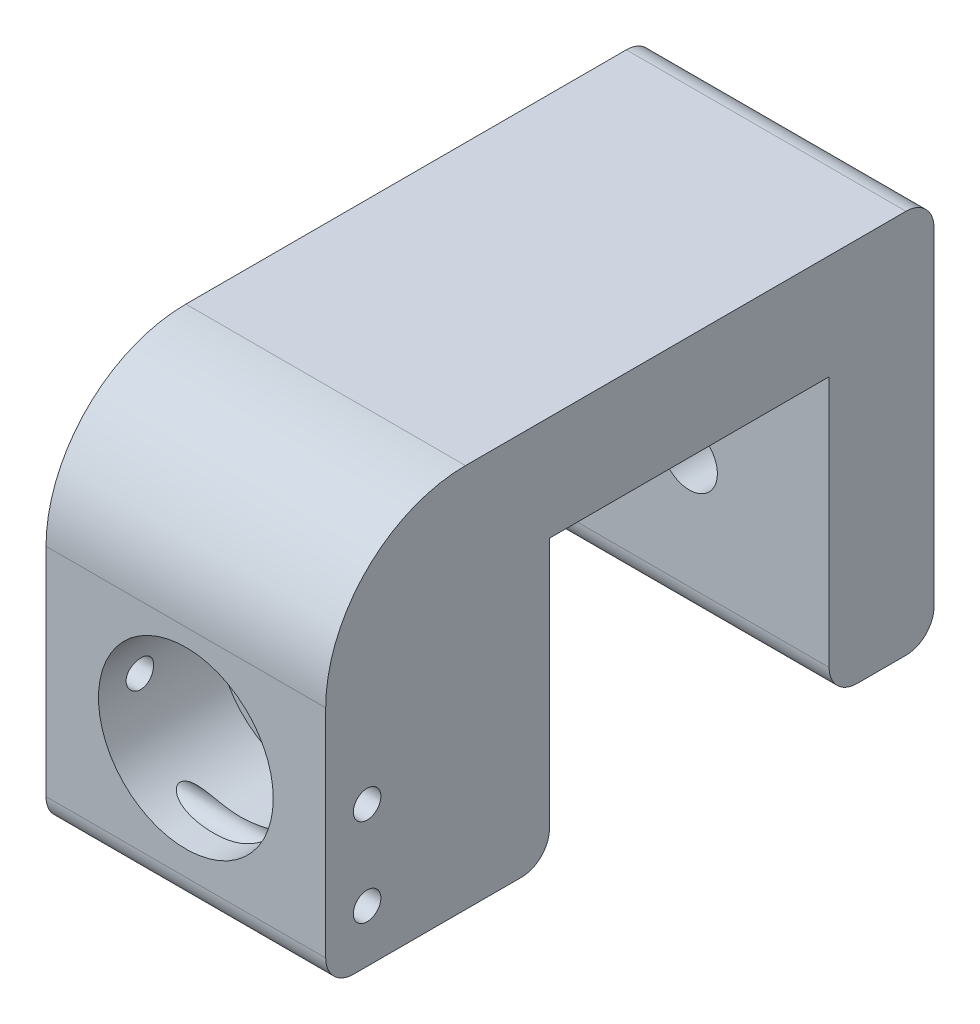
SolidWorks part; units mm, degrees
material "PET"
ref_plane "Front" through (0, 0, 0) normal (0, 0, 1) x (1, 0, 0)
ref_plane "Top" through (0, 0, 0) normal (0, 1, 0) x (1, 0, 0)
ref_plane "Right" through (0, 0, 0) normal (1, 0, 0) x (0, 0, -1)
sketch "Sketch1" plane through (0, 0, 0) normal (1, 0, 0) x (0, 0, -1)
  line L0 (0, 0) -> (0, -25.4)
  line L1 (0, -25.4) -> (-20.32, -25.4)
  line L2 (-20.32, -25.4) -> (-20.32, -3.175)
  line L3 (-7.62, 9.525) -> (34.925, 9.525)
  line L4 (34.925, 9.525) -> (34.925, -25.4)
  line L5 (34.925, -25.4) -> (25.4, -25.4)
  line L6 (25.4, -25.4) -> (25.4, 0)
  line L7 (25.4, 0) -> (0, 0)
  arc A0 (-20.32, -3.175) -> (-7.62, 9.525) centre (-7.62, -3.175) cw
  point P4 (0, 0)
  dimension "D6" = 12.7
  dimension "D1" = 25.4
  dimension "D2" = 25.4
  dimension "D3" = 9.525
  dimension "D4" = 9.525
  dimension "D5" = 20.32
extrude "Boss-Extrude1" add sketch "Sketch1" along normal blind 25.4
sketch "Sketch4" plane through (0, 0, 0) normal (0, 0, -1) x (-1, 0, 0)
  line L0 (-25.4, 0) -> (0, -25.4) construction
  point P0 (-12.7, -12.7)
hole_wizard "1/4 (0.2500) Dowel Hole1" positions "Sketch4" profile "Sketch3" hole size "1/4" standard "ANSI Inch"
sketch "Sketch3" plane through (12.7, -12.7, 0) normal (1, 0, 0) x (0, 1, 0)
  line L0 (0, 0) -> (0, 20.32)
  line L1 (0, 20.32) -> (3.175, 20.32)
  line L2 (3.175, 20.32) -> (3.175, 0)
  line L5 (3.175, 0) -> (0, 0)
  line L11 (0, -6.35) -> (0, 107.95) construction
  dimension "Thru Hole Dia." = 6.35
  dimension "Thru Hole Depth" = 20.32
sketch "Sketch7" plane through (0, 0, -34.925) normal (0, 0, -1) x (-1, 0, 0)
  circle A0 centre (-12.7, -12.7) radius 3.175 construction
  point P0 (-12.7, -12.7)
hole_wizard "#10 Clearance Hole1" positions "Sketch7" profile "Sketch6" hole size "#10" standard "ANSI Inch" end condition through all
sketch "Sketch6" plane through (12.7, -12.7, -34.925) normal (1, 0, 0) x (0, 1, 0)
  line L0 (0, 0) -> (0, 55.245)
  line L1 (0, 55.245) -> (2.5527, 55.245)
  line L2 (2.5527, 55.245) -> (2.5527, 0)
  line L5 (2.5527, 0) -> (0, 0)
  line L11 (0, -6.35) -> (0, 107.95) construction
  dimension "Thru Hole Dia." = 5.1054
  dimension "Thru Hole Depth" = 55.245
sketch "Sketch8" plane through (0, 0, 20.32) normal (0, 0, 1) x (1, 0, 0)
  circle A0 centre (12.7, -12.7) radius 7.9375
  dimension "D1" = 15.875
extrude "Cut-Extrude1" cut sketch "Sketch8" against normal offset from surface (10.795 mm away) 9.525 up to face at (12.7, -9.525, 0)
sketch "Sketch11" plane through (25.4, 0, 0) normal (1, 0, 0) x (0, 0, -1)
  line L5 (0, -25.4) -> (0, 0) construction
  line L8 (-20.32, -25.4) -> (0, -25.4) construction
  point P0 (-16.5608, -12.6375)
  point P2 (-16.5608, -20.6375)
  dimension "D1" = 8
  dimension "D2" = 4.7625
  dimension "D3" = 16.5608
hole_wizard "M3x0.5 Tapped Hole1" positions "Sketch11" profile "Sketch10" tap size "M3x0.5" standard "ANSI Metric" end condition through all
sketch "Sketch10" plane through (25.4, -12.6375, 16.5608) normal (0, 1, 0) x (0, 0, -1)
  line L0 (0, 0) -> (0, 25.4)
  line L1 (0, 25.4) -> (1.25, 25.4)
  line L2 (1.25, 25.4) -> (1.25, 0)
  line L5 (1.25, 0) -> (0, 0)
  line L11 (0, -6.35) -> (0, 107.95) construction
  dimension "Thru Tap Drill Dia." = 2.5
  dimension "Thru Tap Drill Depth" = 25.4
cosmetic thread "Hole Thread1" parameters "D2"=3
cosmetic thread "Hole Thread2" parameters "D2"=3
fillet "Fillet1" radius 2.54 5 edges at (12.7, 9.525, -34.925) (12.7, -25.4, -34.925) (12.7, -25.4, -25.4) (12.7, -25.4, 0) (12.7, -25.4, 20.32)
